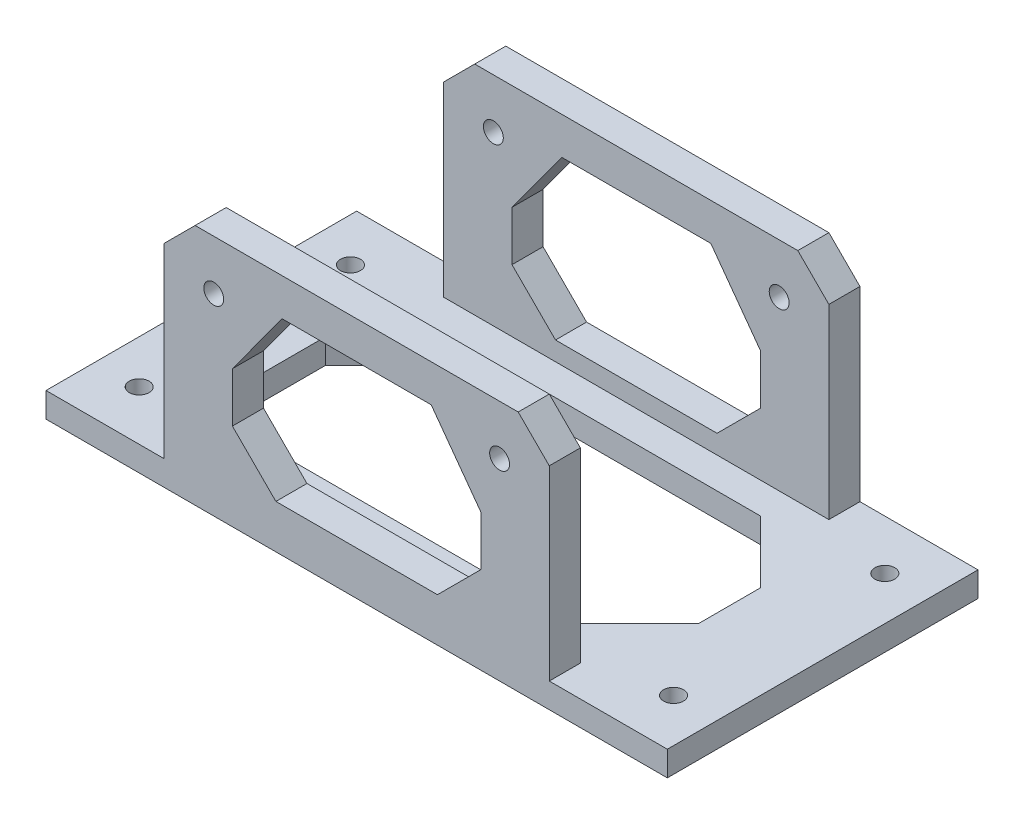
SolidWorks part; units mm, degrees
ref_plane "前视基准面" through (0, 0, 0) normal (0, 0, 1) x (1, 0, 0)
ref_plane "上视基准面" through (0, 0, 0) normal (0, 1, 0) x (1, 0, 0)
ref_plane "右视基准面" through (0, 0, 0) normal (1, 0, 0) x (0, 0, -1)
sketch "草图1" plane through (0, 0, 0) normal (0, 1, 0) x (1, 0, 0)
  line L0 (-50, 0) -> (50, 0) construction
  line L1 (50, -25) -> (-50, -25)
  line L2 (50, -25) -> (50, 25)
  line L3 (50, 25) -> (-50, 25)
  line L4 (-50, -25) -> (-50, 25)
  line L5 (0, 25) -> (0, -25) construction
  circle A0 centre (-43, 17) radius 1.6
  circle A1 centre (-43, -17) radius 1.6
  circle A2 centre (43, -17) radius 1.6
  circle A3 centre (43, 17) radius 1.6
  point P0 (0, 0)
  dimension "D3" = 17
  dimension "D1" = 100
  dimension "D2" = 50
  dimension "D4" = 7
extrude "凸台-拉伸1" add sketch "草图1" along normal blind 4
sketch "草图2" plane through (0, 4, 0) normal (0, 1, 0) x (1, 0, 0)
  line L0 (-50, 0) -> (50, 0) construction
  line L1 (-50, 25) -> (-50, -25) construction
  line L2 (50, -25) -> (50, 25) construction
  line L3 (0, 25) -> (0, -25) construction
  line L4 (50, 25) -> (-50, 25) construction
  line L5 (-50, -25) -> (50, -25) construction
  line L6 (-36, 25) -> (-36, 20)
  line L7 (-36, 20) -> (36, 20)
  line L8 (-36, 25) -> (36, 25)
  line L9 (36, 25) -> (36, 20)
  line L10 (36, -25) -> (36, -20)
  line L11 (-36, -25) -> (36, -25)
  line L12 (-36, -20) -> (36, -20)
  line L13 (-36, -25) -> (-36, -20)
  point P17 (0, 20)
  dimension "D1" = 5
  dimension "D2" = 36
extrude "凸台-拉伸2" add sketch "草图2" along normal blind 35
sketch "草图3" plane through (0, 0, -25) normal (0, 0, -1) x (-1, 0, 0)
  line L0 (0, 39) -> (0, 0) construction
  line L1 (-36, 39) -> (36, 39) construction
  line L2 (-50, 4) -> (-36, 4) construction
  line L3 (-26, 39) -> (-36, 29)
  line L4 (-36, 39) -> (-36, 4) construction
  line L5 (-36, 39) -> (-36, 29)
  line L6 (-36, 39) -> (-26, 39)
  line L7 (36, 39) -> (26, 39)
  line L8 (36, 39) -> (36, 29)
  line L9 (26, 39) -> (36, 29)
  circle A0 centre (-23, 31) radius 1.6
  circle A1 centre (23, 31) radius 1.6
  dimension "D1" = 27
  dimension "D2" = 23
  dimension "D3" = 10
  dimension "D4" = 10
extrude "切除-拉伸1" cut sketch "草图3" against normal through all
sketch "草图4" plane through (0, 0, -25) normal (0, 0, -1) x (-1, 0, 0)
  line L0 (0, 39) -> (0, 0) construction
  line L1 (-26, 39) -> (26, 39) construction
  line L2 (-50, 0) -> (50, 0) construction
  line L3 (12, 33) -> (-12, 33) construction
  line L4 (12, 33) -> (-12, 33)
  line L5 (-20, 22.0354) -> (-20, 7.0354) construction
  line L6 (-20, 7.0354) -> (20, 7.0354) construction
  line L7 (13, 7.0354) -> (-13, 7.0354)
  line L8 (-20, 14.0354) -> (-20, 22.0354)
  line L9 (-20, 22.0354) -> (-12, 33)
  line L10 (20, 22.0354) -> (20, 7.0354) construction
  line L11 (20, 22.0354) -> (12, 33)
  line L12 (20, 14.0354) -> (20, 22.0354)
  line L13 (-20, 14.0354) -> (-13, 7.0354)
  line L14 (20, 14.0354) -> (13, 7.0354)
  line L15 (-36, 4) -> (-31, 4)
  line L16 (-31, 4) -> (-31, 34)
  line L17 (-36, 29) -> (-26, 39) construction
  line L18 (-31, 34) -> (-36, 29)
  line L19 (-36, 29) -> (-36, 4)
  line L20 (31, 34) -> (36, 29)
  line L21 (31, 4) -> (31, 34)
  line L22 (36, 4) -> (31, 4)
  line L23 (36, 29) -> (36, 4)
  point P11 (0, 33)
  point P14 (0, 7.0354)
  dimension "D1" = 6
  dimension "D2" = 12
  dimension "D3" = 20
  dimension "D4" = 15
  dimension "D5" = 7
  dimension "D6" = 7
extrude "切除-拉伸2" cut sketch "草图4" against normal through all
sketch "草图5" plane through (0, 4, 0) normal (0, 1, 0) x (1, 0, 0)
  line L0 (-27.1009, 0) -> (50, 0) construction
  line L1 (-25, 15) -> (-35, 5)
  line L2 (50, -25) -> (50, 25) construction
  line L3 (0, 25) -> (0, -32.3864) construction
  line L4 (26, 25) -> (-26, 25) construction
  line L5 (-35, 5) -> (-35, -5)
  line L6 (-25, 15) -> (25, 15)
  line L7 (35, 5) -> (35, -5)
  line L8 (-25, -15) -> (25, -15)
  line L9 (-25, -15) -> (-35, -5)
  line L10 (25, -15) -> (35, -5)
  line L11 (25, 15) -> (35, 5)
  point P15 (0, 15)
  point P16 (0, -15)
  point P18 (35, 0)
  point P19 (-35, 0)
  dimension "D4" = 10
extrude "切除-拉伸3" cut sketch "草图5" against normal through all
